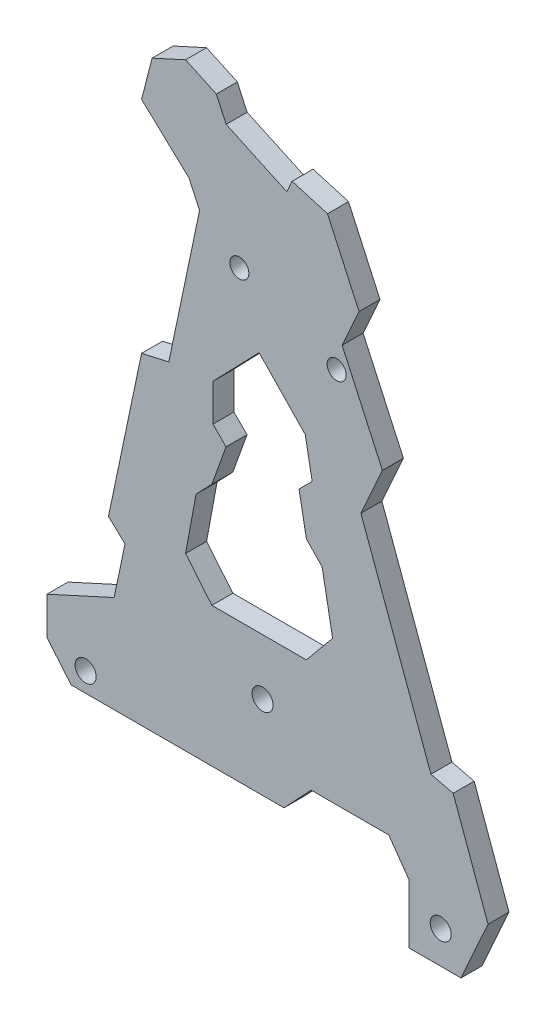
SolidWorks part; units mm, degrees
ref_plane "Front Plane" through (0, 0, 0) normal (0, 0, 1) x (1, 0, 0)
ref_plane "Top Plane" through (0, 0, 0) normal (0, 1, 0) x (1, 0, 0)
ref_plane "Right Plane" through (0, 0, 0) normal (1, 0, 0) x (0, 0, -1)
sketch "Sketch1" plane through (0, 0, 0) normal (0, 0, 1) x (1, 0, 0)
  line L0 (-20.2651, -14.7819) -> (0, -14.7819)
  line L1 (0, -14.7819) -> (2.5782, -12.0317)
  line L2 (2.5782, -12.0317) -> (9.9749, -12.0317)
  line L3 (9.9749, -12.0317) -> (11.9216, -14.7819)
  line L4 (11.9216, -14.7819) -> (11.9216, -20.3872)
  line L5 (11.9216, -20.3872) -> (16.8563, -20.3872)
  line L6 (16.8563, -20.3872) -> (19.4284, -14.6681)
  line L7 (19.4284, -14.6681) -> (16.1096, -5.5265)
  line L8 (16.1096, -5.5265) -> (13.9934, -5.0122)
  line L10 (7.3212, 13.1723) -> (9.3715, 17.7309)
  line L11 (9.3715, 17.7309) -> (5.5334, 26.135)
  line L12 (5.5334, 26.135) -> (7.1436, 29.7152)
  line L13 (7.1436, 29.7152) -> (4.144, 36.2834)
  line L14 (4.144, 36.2834) -> (0.7716, 37.2745)
  line L15 (0.7716, 37.2745) -> (0.2699, 36.1589)
  line L16 (0.2699, 36.1589) -> (-5.5114, 38.8258)
  line L17 (-5.5114, 38.8258) -> (-6.442, 40.8636)
  line L18 (-6.442, 40.8636) -> (-9.3784, 42.2181)
  line L19 (-9.3784, 42.2181) -> (-12.5617, 40.7643)
  line L20 (-12.5617, 40.7643) -> (-13.5635, 36.8653)
  line L21 (-13.5635, 36.8653) -> (-9.0348, 32.6196)
  line L22 (-9.0348, 32.6196) -> (-8.0448, 30.4518)
  line L23 (-8.0448, 30.4518) -> (-10.9701, 16.5041)
  line L24 (-10.9701, 16.5041) -> (-13.5635, 15.9198)
  line L25 (-13.5635, 15.9198) -> (-16.7159, 0.8893)
  line L26 (-16.7159, 0.8893) -> (-15.1397, -0.5884)
  line L27 (-15.1397, -0.5884) -> (-16.1754, -5.5265)
  line L28 (-16.1754, -5.5265) -> (-22.5716, -8.4476)
  line L29 (-22.5716, -8.4476) -> (-22.5716, -12.0317)
  line L30 (-22.5716, -12.0317) -> (-20.2651, -14.7819)
  line L31 (0, -14.7819) -> (11.9216, -14.7819) construction
  line L32 (13.9934, -5.0122) -> (7.3212, 13.1723)
  line L33 (2.1287, -1.5188) -> (-6.8713, -1.5188)
  line L34 (-6.8713, -1.5188) -> (-9.3713, 1.5104)
  line L35 (-9.3713, 1.5104) -> (-8.3713, 6.9086)
  line L36 (-8.3713, 6.9086) -> (-6.8713, 8.4635)
  line L37 (-6.8713, 8.4635) -> (-5.5197, 12.2283)
  line L38 (-5.5197, 12.2283) -> (-6.7697, 13.4782)
  line L39 (-6.7697, 13.4782) -> (-6.7697, 17.0095)
  line L40 (-6.7697, 17.0095) -> (-2.3713, 21.569)
  line L41 (-2.3713, 21.569) -> (2.0271, 17.0095)
  line L42 (2.0271, 17.0095) -> (2.6812, 13.4782)
  line L43 (2.6812, 13.4782) -> (1.4313, 12.2283)
  line L44 (1.4313, 12.2283) -> (2.1287, 8.4635)
  line L45 (2.1287, 8.4635) -> (3.6287, 6.9086)
  line L46 (3.6287, 6.9086) -> (4.6287, 1.5104)
  line L47 (4.6287, 1.5104) -> (2.1287, -1.5188)
  line L48 (-9.3713, 1.5104) -> (4.6287, 1.5104) construction
  line L49 (3.6287, 6.9086) -> (-8.3713, 6.9086) construction
  line L50 (-6.8713, 8.4635) -> (2.1287, 8.4635) construction
  line L51 (1.4313, 12.2283) -> (-5.5197, 12.2283) construction
  line L52 (-6.7697, 13.4782) -> (2.6812, 13.4782) construction
  line L53 (2.0271, 17.0095) -> (-6.7697, 17.0095) construction
  line L54 (-2.3713, -1.5188) -> (-2.3713, 1.5104) construction
  line L55 (-2.3713, 1.5104) -> (-2.3713, 6.9086) construction
  line L56 (-2.3713, 6.9086) -> (-2.3713, 8.4635) construction
  line L57 (-2.3713, 8.4635) -> (-2.0442, 12.2283) construction
  line L58 (-2.0442, 12.2283) -> (-2.0442, 13.4782) construction
  line L59 (-2.0442, 13.4782) -> (-2.3713, 17.0095) construction
  line L60 (-2.3713, 17.0095) -> (-2.3713, 21.569) construction
  line L61 (5.0157, 23.8657) -> (-4.2547, 27.6154) construction
  circle A0 centre (-18.8927, -12.9289) radius 1
  circle A1 centre (14.9216, -17.2819) radius 1
  circle A2 centre (-2.0442, -6.8424) radius 1
  circle A3 centre (5.0157, 23.8657) radius 0.9102
  circle A4 centre (-4.2547, 27.6154) radius 0.906
  dimension "D3" = 3
  dimension "D1" = 57
  dimension "D2" = 42
  dimension "D4" = 2.5
  dimension "D5" = 14
  dimension "D6" = 9
  dimension "D7" = 9
  dimension "D8" = 12
  dimension "D9" = 10
extrude "Boss-Extrude1" add sketch "Sketch1" along normal blind 2
